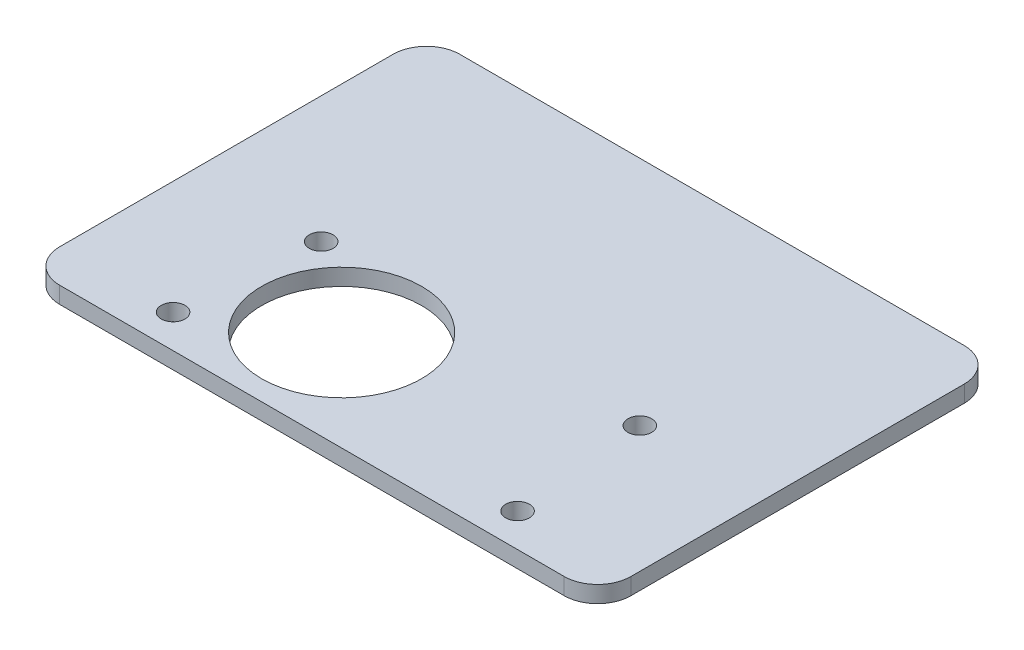
SolidWorks part; units mm, degrees
ref_plane "前视基准面" through (0, 0, 0) normal (0, 0, 1) x (1, 0, 0)
ref_plane "上视基准面" through (0, 0, 0) normal (0, 1, 0) x (1, 0, 0)
ref_plane "右视基准面" through (0, 0, 0) normal (1, 0, 0) x (0, 0, -1)
ref_plane "基准面4" through (0, -4.7625, 0) normal (0, -1, 0) x (1, 0, 0)
sketch "草图1" plane through (0, -4.7625, 0) normal (0, -1, 0) x (1, 0, 0)
  line L0 (33.9, -25.4) -> (33.9, 6.35)
  line L1 (30.725, 9.525) -> (-17.325, 9.525)
  line L2 (-20.5, 6.35) -> (-20.5, -25.4)
  line L3 (-17.325, -28.575) -> (30.725, -28.575)
  arc A0 (33.9, 6.35) -> (30.725, 9.525) centre (30.725, 6.35) ccw
  arc A1 (-17.325, 9.525) -> (-20.5, 6.35) centre (-17.325, 6.35) ccw
  arc A2 (-20.5, -25.4) -> (-17.325, -28.575) centre (-17.325, -25.4) ccw
  arc A3 (30.725, -28.575) -> (33.9, -25.4) centre (30.725, -25.4) ccw
  circle A4 centre (0, 0) radius 7.62
  circle A5 centre (-9.705, 6.35) radius 1.1303
  circle A6 centre (23.105, 6.35) radius 1.1303
  circle A7 centre (21.875, -6.525) radius 1.1303
  circle A8 centre (-8.475, -6.525) radius 1.1303
extrude "凸台-拉伸1" add sketch "草图1" against normal blind 1.5875
